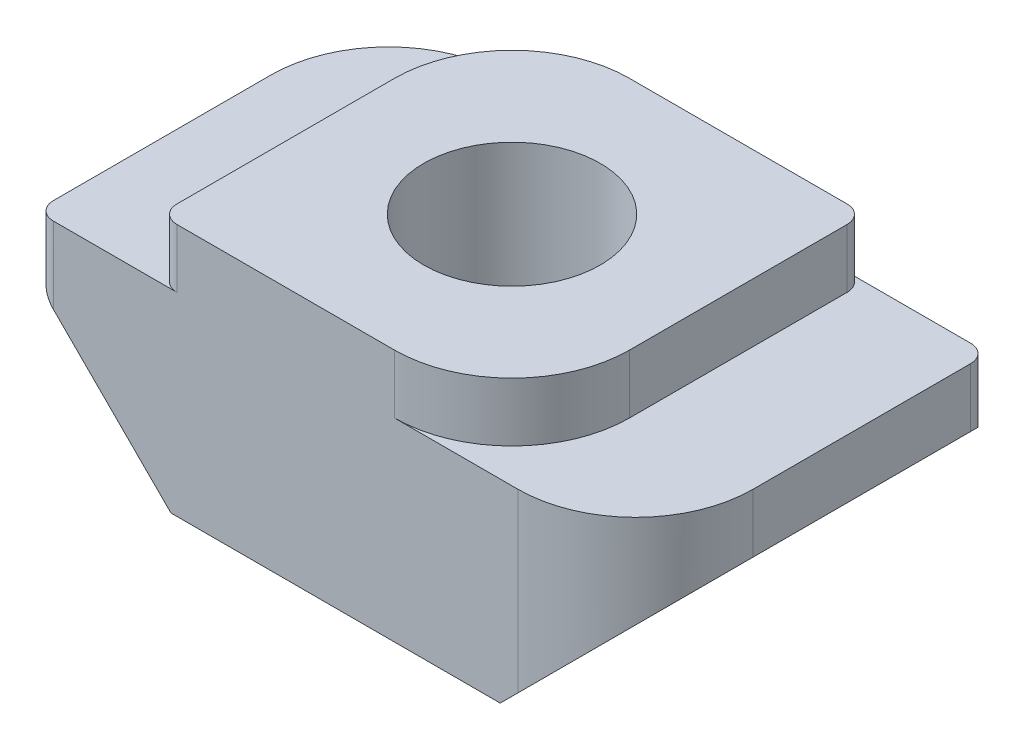
SolidWorks part; units mm, degrees
material "不锈钢 (铁素体)"
ref_plane "前视基准面" through (0, 0, 0) normal (0, 0, 1) x (1, 0, 0)
ref_plane "上视基准面" through (0, 0, 0) normal (0, 1, 0) x (1, 0, 0)
ref_plane "右视基准面" through (0, 0, 0) normal (1, 0, 0) x (0, 0, -1)
sketch "草图1" plane through (0, 0, 0) normal (0, 0, 1) x (1, 0, 0)
  line L0 (0, 0) -> (0, 8533.2886) construction
  line L1 (-3, 4.3) -> (3, 4.3)
  line L2 (3, 4.3) -> (3, 3.3)
  line L3 (3, 3.3) -> (5.1, 3.3)
  line L4 (5.1, 3.3) -> (5.1, 2.3)
  line L5 (5.1, 2.3) -> (2.8, 0)
  line L6 (2.8, 0) -> (-2.8, 0)
  line L7 (-5.1, 2.3) -> (-2.8, 0)
  line L8 (-5.1, 3.3) -> (-5.1, 2.3)
  line L9 (-3, 3.3) -> (-5.1, 3.3)
  line L10 (-3, 4.3) -> (-3, 3.3)
  point P11 (0, 0)
  point P15 (0, 4.3)
  dimension "D1" = 3.3
  dimension "D2" = 10.2
  dimension "D3" = 4.3
  dimension "D4" = 45
  dimension "D5" = 1
  dimension "D6" = 6
extrude "凸台-拉伸1" add sketch "草图1" along normal blind 6
fillet "圆角1" radius 2 2 edges at (3, 3.8, 6) (-3, 3.8, 0)
fillet "圆角2" radius 2 2 edges at (5.1, 2.8, 6) (-5.1, 2.8, 0)
fillet "圆角3" radius 0.3 4 edges at (-5.1, 2.8, 6) (-3, 3.8, 6) (3, 3.8, 0) (5.1, 2.8, 0)
sketch "草图2" plane through (0, 4.3, 0) normal (0, 1, 0) x (1, 0, 0)
  circle A0 centre (0, -3) radius 1.5
  dimension "D1" = 3
  dimension "D2" = 3
extrude "切除-拉伸1" cut sketch "草图2" against normal blind 6
